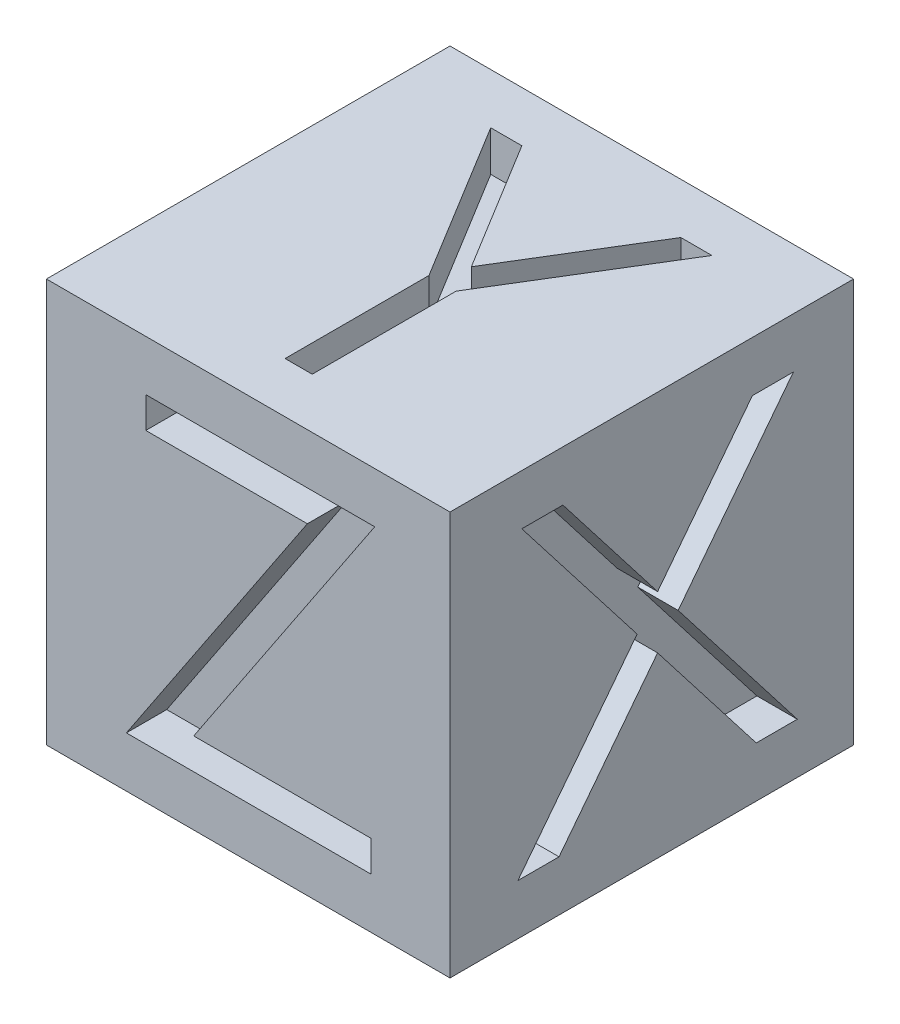
SolidWorks part; units mm, degrees
ref_plane "Front Plane" through (0, 0, 0) normal (0, 0, 1) x (1, 0, 0)
ref_plane "Top Plane" through (0, 0, 0) normal (0, 1, 0) x (1, 0, 0)
ref_plane "Right Plane" through (0, 0, 0) normal (1, 0, 0) x (0, 0, -1)
sketch "Sketch1" plane through (0, 0, 0) normal (0, 1, 0) x (1, 0, 0)
  line L1 (10, -10) -> (-10, -10)
  line L2 (10, -10) -> (10, 10)
  line L3 (10, 10) -> (-10, 10)
  line L4 (-10, -10) -> (-10, 10)
  line L5 (10, -10) -> (-10, 10) construction
  line L6 (10, 10) -> (-10, -10) construction
  point P0 (0, 0)
  dimension "D1" = 20
extrude "Boss-Extrude1" add sketch "Sketch1" along normal blind 20
sketch "Sketch2" plane through (0, 0, 10) normal (0, 0, 1) x (1, 0, 0)
  text T0 "Z" font "Century Gothic" height 15
  point P1 (-1.3905, 9.7639)
  point P2 (-2.23, 8.6882)
  point P3 (0, 0)
  point P4 (0, 0)
  point P5 (-2.4399, 6.2746)
  point P6 (-5.1159, 4.097)
  point P7 (0, 0)
  point P8 (0, 0)
  point P11 (0, 0)
extrude "Cut-Extrude1" cut sketch "Sketch2" against normal blind 2
sketch "Sketch3" plane through (10, 0, 0) normal (1, 0, 0) x (0, 0, -1)
  text T0 "X" font "Century Gothic" height 15
  point P1 (0, 0)
  point P2 (0, 0)
extrude "Cut-Extrude2" cut sketch "Sketch3" against normal blind 2
sketch "Sketch4" plane through (0, 20, 0) normal (0, 1, 0) x (1, 0, 0)
  text T0 "Y" font "Century Gothic" height 15
  point P1 (0, 0)
extrude "Cut-Extrude3" cut sketch "Sketch4" against normal blind 2
